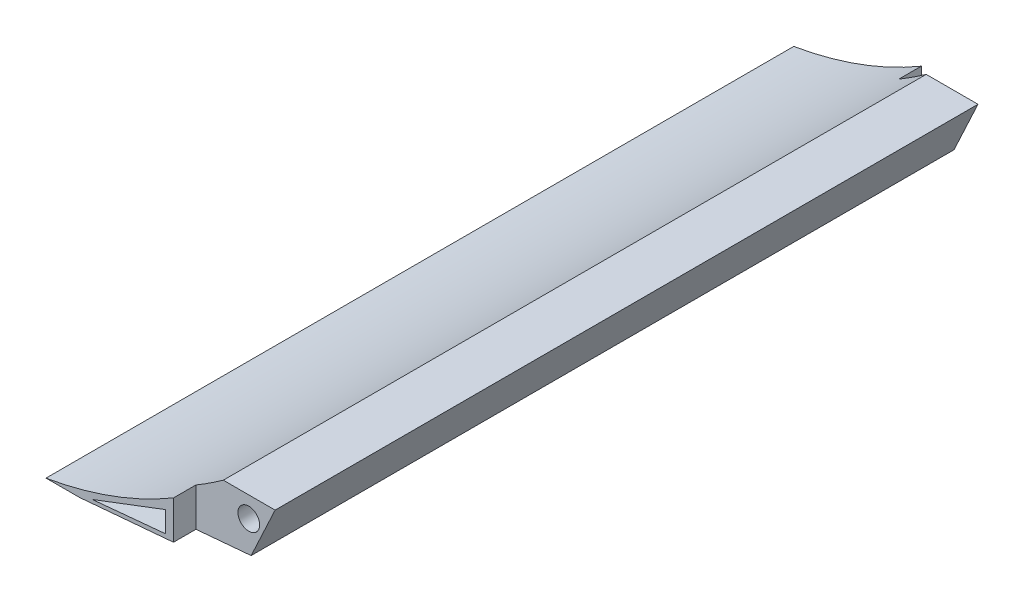
SolidWorks part; units mm, degrees
ref_plane "Front Plane" through (0, 0, 0) normal (0, 0, 1) x (1, 0, 0)
ref_plane "Top Plane" through (0, 0, 0) normal (0, 1, 0) x (1, 0, 0)
ref_plane "Right Plane" through (0, 0, 0) normal (1, 0, 0) x (0, 0, -1)
sketch "Sketch1" plane through (0, 0, 0) normal (0, 0, 1) x (1, 0, 0)
  line L1 (24.4345, 1.7431) -> (35, 24.4008)
  line L2 (-12.3829, 0) -> (49.6644, 0) construction
  line L3 (0, 0) -> (4.5106, 0)
  line L4 (4.5106, 0) -> (24.4345, 1.7431)
  arc A0 (0, 0) -> (35, 24.4008) centre (-8.3617, 49.2959) ccw
  dimension "D4" = 50
  dimension "D1" = 20
  dimension "D2" = 5
  dimension "D3" = 25
  dimension "D5" = 35
  dimension "D6" = 120
extrude "Extrude1" add sketch "Sketch1" along normal blind 100
sketch "Sketch10" plane through (0, 0, 100) normal (0, 0, 1) x (1, 0, 0)
  line L0 (27.0844, 11.4268) -> (29.0844, 11.0667)
  line L2 (27.0844, 11.4268) -> (17.0542, 3.072)
  line L3 (17.0542, 3.072) -> (24.4345, 1.7431)
  line L4 (29.0844, 11.0667) -> (24.4345, 1.7431)
  dimension "D1" = 10
  dimension "D2" = 50
  dimension "D3" = 13.0541
  dimension "D4" = 2
extrude "Extrude5" cut sketch "Sketch10" against normal blind 3
ref_plane "Plane2" through (0, 0, 50) normal (0, 0, 1) x (1, 0, 0)
mirror "Mirror2" about plane through (0, 0, 50) normal (0, 0, 1) of "Extrude5"
sketch "Sketch13" plane through (0, 0, 97) normal (0, 0, 1) x (1, 0, 0)
  line L0 (27.0844, 11.4268) -> (17.0542, 3.072) construction
  line L1 (24.4345, 1.7431) -> (28.8056, 11.1169) construction
  line L2 (17.0542, 3.072) -> (24.4345, 1.7431) construction
  circle A0 centre (24.1201, 5.8641) radius 1.5
  point P4 (26.6201, 6.43)
  dimension "D1" = 4
  dimension "D2" = 2.5
  dimension "D3" = 3
  dimension "D4" = 2.377
hole_wizard "M2.5 Clearance Hole2" positions "3DSketch5" profile "Sketch16" hole size "M2.5" standard "Ansi Metric"
sketch3d "3DSketch5"
  point P0 (24.1201, 5.8641, 97)
sketch "Sketch16" plane through (24.1201, 5.8641, 97) normal (1, 0, 0) x (0, -1, 0)
  line L0 (0, 0) -> (0, 16.8712)
  line L1 (0, 16.8712) -> (1.45, 16)
  line L2 (1.45, 16) -> (1.45, 0)
  line L5 (1.45, 0) -> (0, 0)
  line L10 (0, 16.8712) -> (-1.45, 16) construction
  line L11 (0, -6.35) -> (0, 107.95) construction
  dimension "Hole Dia." = 2.9
  dimension "Hole Depth" = 16
  dimension "Drill Angle" = 118
mirror "Mirror3" about plane through (0, 0, 50) normal (0, 0, 1) of "M2.5 Clearance Hole2"
sketch "Sketch17" plane through (0, 0, 100) normal (0, 0, 1) x (1, 0, 0)
  line L5 (0, 11.1169) -> (35, 11.1169)
  line L6 (0, 11.1169) -> (0, 24.4008)
  line L7 (0, 24.4008) -> (35, 24.4008)
  line L8 (35, 11.1169) -> (35, 24.4008)
extrude "Cut-Extrude1" cut sketch "Sketch17" against normal blind 100
sketch "Sketch19" plane through (0, 0, 100) normal (0, 0, 1) x (1, 0, 0)
  line L1 (28.8056, 11.1169) -> (3.9074, 11.1169)
  line L2 (28.8056, 11.1169) -> (28.8056, 8.6169)
  line L3 (28.8056, 8.6169) -> (3.9074, 8.6169)
  line L4 (3.9074, 11.1169) -> (3.9074, 8.6169)
  dimension "D1" = 2.5
extrude "Cut-Extrude2" cut sketch "Sketch19" against normal blind 100
sketch "Sketch20" plane through (0, 0, 100) normal (0, 0, 1) x (1, 0, 0)
  line L0 (6.187, 0.6203) -> (15.9485, 4.3305)
  line L1 (15.9485, 4.3305) -> (15.9485, 1.5437)
  line L2 (15.9485, 1.5437) -> (6.187, 0.6203)
extrude "Cut-Extrude3" cut sketch "Sketch20" against normal blind 98
sketch "Sketch21" plane through (0, 0, 100) normal (0, 0, 1) x (1, 0, 0)
  line L1 (17.0542, 3.072) -> (23.7111, 3.072)
  line L2 (17.0542, 3.072) -> (17.0542, 8.6169)
  line L3 (17.0542, 8.6169) -> (23.7111, 8.6169)
  line L4 (23.7111, 3.072) -> (23.7111, 8.6169)
extrude "Cut-Extrude5" cut sketch "Sketch21" against normal blind 3
sketch "Sketch23" plane through (0, 0, 100) normal (0, 0, 1) x (1, 0, 0)
  line L1 (17.0542, 3.072) -> (28.3184, 3.072)
  line L2 (17.0542, 3.072) -> (17.0542, 0)
  line L3 (17.0542, 0) -> (28.3184, 0)
  line L4 (28.3184, 3.072) -> (28.3184, 0)
extrude "Cut-Extrude6" cut sketch "Sketch23" against normal blind 3
sketch "Sketch24" plane through (0, 0, 0) normal (0, 0, -1) x (-1, 0, 0)
  line L1 (-23.7111, 8.6169) -> (-17.0542, 8.6169)
  line L2 (-23.7111, 8.6169) -> (-23.7111, 3.072)
  line L3 (-23.7111, 3.072) -> (-17.0542, 3.072)
  line L4 (-17.0542, 8.6169) -> (-17.0542, 3.072)
extrude "Cut-Extrude7" cut sketch "Sketch24" against normal blind 3
sketch "Sketch25" plane through (0, 0, 0) normal (0, 0, -1) x (-1, 0, 0)
  line L1 (-17.0542, 3.072) -> (-25.1832, 3.072)
  line L2 (-17.0542, 3.072) -> (-17.0542, -2.3378)
  line L3 (-17.0542, -2.3378) -> (-25.1832, -2.3378)
  line L4 (-25.1832, 3.072) -> (-25.1832, -2.3378)
extrude "Cut-Extrude8" cut sketch "Sketch25" against normal blind 3
sketch "Sketch28" plane through (0.0343, -0.3916, 0) normal (0.0872, -0.9962, 0) x (-0.9962, -0.0872, 0)
  circle A0 centre (-14.6716, -47.4638) radius 0.6
